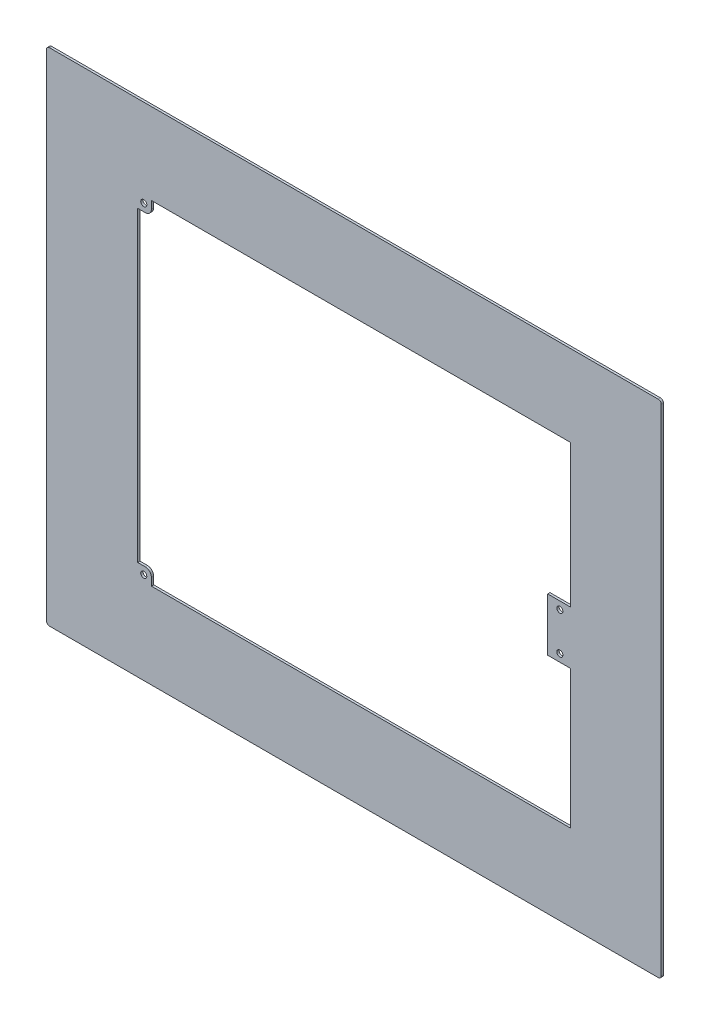
SolidWorks part; units mm, degrees
ref_plane "Front Plane" through (0, 0, 0) normal (0, 0, 1) x (1, 0, 0)
ref_plane "Top Plane" through (0, 0, 0) normal (0, 1, 0) x (1, 0, 0)
ref_plane "Right Plane" through (0, 0, 0) normal (1, 0, 0) x (0, 0, -1)
sketch "Sketch1" plane through (0, 0, 0) normal (0, 0, 1) x (1, 0, 0)
  line L1 (-202.5, -165) -> (202.5, -165)
  line L2 (-202.5, -165) -> (-202.5, 165)
  line L3 (-202.5, 165) -> (202.5, 165)
  line L4 (202.5, -165) -> (202.5, 165)
  line L5 (-202.5, -165) -> (202.5, 165) construction
  line L6 (-202.5, 165) -> (202.5, -165) construction
  point P0 (0, 0)
  dimension "D1" = 405
  dimension "D2" = 330
extrude "Boss-Extrude1" add sketch "Sketch1" along normal blind 1.5
sketch "Sketch2" plane through (0, 0, 1.5) normal (0, 0, 1) x (1, 0, 0)
  line L0 (0, 0) -> (0, 176.6374) construction
  line L1 (0, 0) -> (235.7395, 0) construction
  line L3 (-142.41, 111.43) -> (142.71, 111.43)
  line L4 (-142.41, 111.43) -> (-142.41, -108.6)
  line L5 (-142.41, -108.6) -> (142.71, -108.6)
  line L6 (142.71, 111.43) -> (142.71, -108.6)
  dimension "D1" = 142.41
  dimension "D2" = 142.71
  dimension "D3" = 285.12
  dimension "D4" = 111.43
  dimension "D5" = 108.6
extrude "Cut-Extrude1" cut sketch "Sketch2" against normal through all
sketch "Sketch3" plane through (0, 0, 1.5) normal (0, 0, 1) x (1, 0, 0)
  line L0 (0, 0) -> (171.1026, 0) construction
  line L1 (-142.41, 111.43) -> (-133.41, 111.43)
  line L2 (-142.41, 111.43) -> (-142.41, 102.43)
  line L3 (-142.41, 102.43) -> (-133.41, 102.43)
  line L4 (-133.41, 111.43) -> (-133.41, 102.43)
  line L5 (-142.41, -108.6) -> (-133.41, -108.6)
  line L6 (-142.41, -108.6) -> (-142.41, -99.6)
  line L7 (-142.41, -99.6) -> (-133.41, -99.6)
  line L8 (-133.41, -108.6) -> (-133.41, -99.6)
  line L9 (142.71, -108.6) -> (142.71, 111.43) construction
  line L10 (142.71, 17.5) -> (127.71, 17.5)
  line L11 (142.71, 17.5) -> (142.71, -17.5)
  line L12 (142.71, -17.5) -> (127.71, -17.5)
  line L13 (127.71, 17.5) -> (127.71, -17.5)
  dimension "D1" = 9
  dimension "D2" = 17.5
  dimension "D3" = 17.5
  dimension "D5" = 15
extrude "Boss-Extrude2" add sketch "Sketch3" against normal up to surface (1.5 mm away) up to face at (0.15, 1.415, 0)
sketch "Sketch4" plane through (0, 0, 1.5) normal (0, 0, 1) x (1, 0, 0)
  line L0 (-142.41, 102.43) -> (-142.41, -99.6) construction
  line L1 (-142.41, 111.43) -> (-138.41, 111.43) construction
  line L2 (-142.41, 111.43) -> (-142.41, 107.43) construction
  line L3 (-142.41, 107.43) -> (-138.41, 107.43) construction
  line L4 (-138.41, 111.43) -> (-138.41, 107.43) construction
  line L5 (142.71, 111.43) -> (-133.41, 111.43) construction
  line L6 (-133.41, -108.6) -> (142.71, -108.6) construction
  line L7 (-142.41, -104.6) -> (-138.41, -104.6) construction
  line L8 (-142.41, -104.6) -> (-142.41, -108.6) construction
  line L9 (-142.41, -108.6) -> (-138.41, -108.6) construction
  line L10 (-138.41, -104.6) -> (-138.41, -108.6) construction
  line L11 (0, 0) -> (154.1113, 0) construction
  line L12 (142.71, -108.6) -> (142.71, -17.5) construction
  circle A0 centre (-138.41, 107.43) radius 2
  circle A1 centre (-138.41, -104.6) radius 2
  circle A2 centre (135.71, 12.5) radius 2
  circle A3 centre (135.71, -12.5) radius 2
  dimension "D1" = 4
  dimension "D2" = 25
  dimension "D3" = 7
  dimension "D4" = 4
extrude "Cut-Extrude2" cut sketch "Sketch4" against normal through all
fillet "Fillet1" radius 4 2 edges at (-133.41, -99.6, 0.75) (-133.41, 102.43, 0.75)
fillet "Fillet2" radius 2 4 edges at (-202.5, 165, 0.75) (202.5, 165, 0.75) (202.5, -165, 0.75) (-202.5, -165, 0.75)
